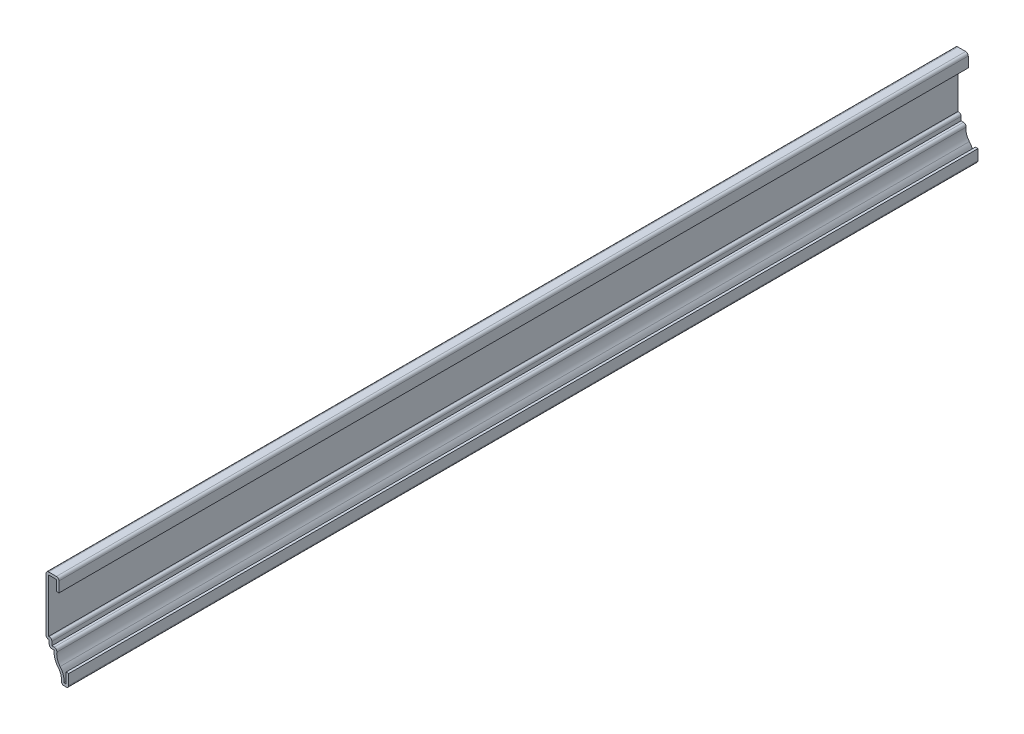
SolidWorks part; units mm, degrees
ref_plane "Front Plane" through (0, 0, 0) normal (0, 0, 1) x (1, 0, 0)
ref_plane "Top Plane" through (0, 0, 0) normal (0, 1, 0) x (1, 0, 0)
ref_plane "Right Plane" through (0, 0, 0) normal (1, 0, 0) x (0, 0, -1)
sketch "Sketch1" plane through (0, 0, 0) normal (0, 0, 1) x (1, 0, 0)
  line L0 (0, 6.35) -> (0, 0)
  line L1 (0, 0) -> (-3.9688, 0)
  line L2 (-7.0701, 12.7) -> (-9.525, 12.7)
  line L3 (-9.525, 12.7) -> (-9.525, 15.875)
  line L4 (-9.525, 15.875) -> (-11.1125, 15.875)
  line L5 (-11.1125, 15.875) -> (-11.1125, 44.45)
  line L6 (-11.1125, 44.45) -> (-4.7625, 44.45)
  line L7 (-4.7625, 44.45) -> (-4.7625, 38.1)
  arc A0 (-3.9688, 0) -> (-5.165, 6.3774) centre (-9.932, 2.1824) ccw
  arc A1 (-5.165, 6.3774) -> (-7.0701, 12.7) centre (0.7938, 11.6212) cw
  point P14 (0, 0)
  point P15 (-4.4282, 5.9286)
  point P16 (-4.9655, 7.3558)
  point P17 (0.7938, 10.7861)
  point P18 (-5.6602, 10.1759)
  point P19 (0, 0)
  point P20 (0.7938, 10.7077)
  point P21 (-5.2558, 5.7805)
extrude "Extrude-Thin1" add sketch "Sketch1" against normal blind 444.5 thin
fillet "Fillet1" radius 1.27 8 edges at (0, 0, -222.25) (-3.9688, 0, -222.25) (-5.4463, 13.97, -222.25) (-9.525, 12.7, -222.25) (-8.255, 17.145, -222.25) (-11.1125, 15.875, -222.25) (-11.1125, 44.45, -222.25) (-4.7625, 44.45, -222.25)
equation "\"D1@Extrude-Thin1\"=\"D11@Sketch1\"*10"
